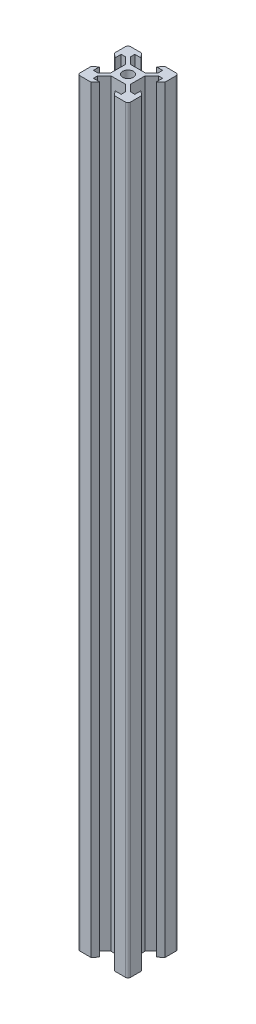
SolidWorks part; units mm, degrees
ref_plane "Front Plane" through (0, 0, 0) normal (0, 0, 1) x (1, 0, 0)
ref_plane "Top Plane" through (0, 0, 0) normal (0, 1, 0) x (1, 0, 0)
ref_plane "Right Plane" through (0, 0, 0) normal (1, 0, 0) x (0, 0, -1)
sketch "Sketch1" plane through (0, 0, 0) normal (0, 1, 0) x (1, 0, 0)
  line L0 (-3.125, 8.2) -> (-4.58, 10)
  line L1 (-9, 10) -> (9, 10)
  line L2 (-10, 9) -> (-10, -9)
  line L3 (-9, -10) -> (9, -10)
  line L4 (10, 9) -> (10, -9)
  line L5 (-10, 10) -> (10, -10) construction
  line L6 (-10, -10) -> (10, 10) construction
  line L7 (-10, 0) -> (0, 0) construction
  line L8 (0, 10) -> (0, 0) construction
  line L9 (-8.2, 3.125) -> (-10, 4.58)
  line L10 (-8.2, 3.125) -> (-8.2, 5.5)
  line L11 (-3.125, 8.2) -> (-5.5, 8.2)
  line L12 (-5.5, 8.2) -> (-5.5, 6.56)
  line L13 (-2.84, 3.9) -> (2.84, 3.9)
  line L14 (-5.5, 6.56) -> (-2.84, 3.9)
  line L15 (-8.2, 5.5) -> (-6.56, 5.5)
  line L16 (-6.56, 5.5) -> (-3.9, 2.84)
  line L17 (-3.9, 2.84) -> (-3.9, -2.84)
  line L18 (3.9, 2.84) -> (3.9, -2.84)
  line L19 (6.56, 5.5) -> (3.9, 2.84)
  line L20 (8.2, 5.5) -> (6.56, 5.5)
  line L21 (8.2, 3.125) -> (8.2, 5.5)
  line L22 (8.2, 3.125) -> (10, 4.58)
  line L23 (3.125, 8.2) -> (4.58, 10)
  line L24 (3.125, 8.2) -> (5.5, 8.2)
  line L25 (5.5, 8.2) -> (5.5, 6.56)
  line L26 (5.5, 6.56) -> (2.84, 3.9)
  line L27 (-8.2, -3.125) -> (-10, -4.58)
  line L28 (-8.2, -3.125) -> (-8.2, -5.5)
  line L29 (-8.2, -5.5) -> (-6.56, -5.5)
  line L30 (-6.56, -5.5) -> (-3.9, -2.84)
  line L31 (8.2, -3.125) -> (10, -4.58)
  line L32 (8.2, -3.125) -> (8.2, -5.5)
  line L33 (8.2, -5.5) -> (6.56, -5.5)
  line L34 (6.56, -5.5) -> (3.9, -2.84)
  line L35 (5.5, -6.56) -> (2.84, -3.9)
  line L36 (5.5, -8.2) -> (5.5, -6.56)
  line L37 (3.125, -8.2) -> (5.5, -8.2)
  line L38 (3.125, -8.2) -> (4.58, -10)
  line L39 (-5.5, -6.56) -> (-2.84, -3.9)
  line L40 (-2.84, -3.9) -> (2.84, -3.9)
  line L41 (-5.5, -8.2) -> (-5.5, -6.56)
  line L42 (-3.125, -8.2) -> (-5.5, -8.2)
  line L43 (-3.125, -8.2) -> (-4.58, -10)
  circle A0 centre (0, 0) radius 2.1
  arc A1 (-10, -9) -> (-9, -10) centre (-9, -9) ccw
  arc A2 (9, -10) -> (10, -9) centre (9, -9) ccw
  arc A3 (9, 10) -> (10, 9) centre (9, 9) cw
  arc A4 (-9, 10) -> (-10, 9) centre (-9, 9) ccw
  point P0 (0, 0)
  point P35 (0, 3.9)
  point P40 (-3.9, 0)
  point P41 (3.9, 0)
  dimension "D3" = 4.2
  dimension "D2" = 1
  dimension "D1" = 20
  dimension "D4" = 6.1
  dimension "D5" = 6.25
  dimension "D6" = 11
  dimension "D7" = 5.68
  dimension "D8" = 9.16
  dimension "D9" = 1.8
extrude "Boss-Extrude1" add sketch "Sketch1" along normal blind 300 contours L43 L42 L41 L39 L40 L35 L36 L37 L38 L3 L4 L31 L32 L33 L34 L18 L19 L20 L21 L22 L1 L23 L24 L25 L26 L13 L14 L12 L11 L0 L2 L9 L10 L15 L16 L17 L30 L29 L28 L27 A0
